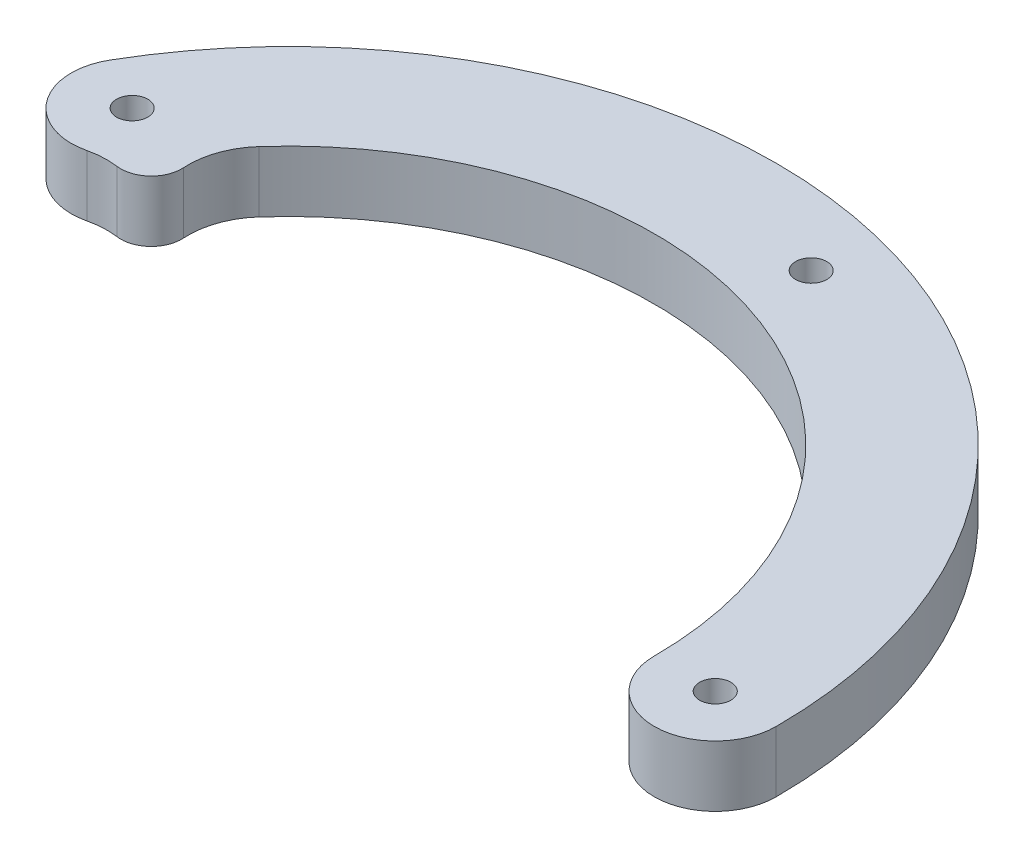
SolidWorks part; units mm, degrees
ref_plane "Front Plane" through (0, 0, 0) normal (0, 0, 1) x (1, 0, 0)
ref_plane "Top Plane" through (0, 0, 0) normal (0, 1, 0) x (1, 0, 0)
ref_plane "Right Plane" through (0, 0, 0) normal (1, 0, 0) x (0, 0, -1)
sketch "Sketch1" plane through (0, 0, 0) normal (0, 1, 0) x (1, 0, 0)
  line L3 (0, 0) -> (-30.84, 17.8055) construction
  line L4 (0, 0) -> (44.45, 0) construction
  line L5 (0, 0) -> (11.5045, 42.9354) construction
  line L6 (-35.7452, 20.6375) -> (-38.4948, 22.225) construction
  arc A0 (50.8, 0) -> (-43.9941, 25.4) centre (0, 0) ccw
  arc A1 (38.1, 0) -> (-28.4399, 25.3531) centre (0, 0) ccw
  circle A2 centre (0, 0) radius 38.1 construction
  circle A3 centre (0, 0) radius 50.8 construction
  arc A4 (-43.9941, 25.4) -> (-37.0197, 16.0487) centre (-38.4948, 22.225) ccw
  arc A5 (38.1, 0) -> (50.8, 0) centre (44.45, 0) ccw
  circle A6 centre (-38.4948, 22.225) radius 1.625
  circle A7 centre (44.45, 0) radius 1.625
  circle A8 centre (0, 0) radius 44.45 construction
  circle A9 centre (11.5045, 42.9354) radius 1.625
  arc A10 (-34.0591, 16.1913) -> (-30.4528, 19.5331) centre (-33.6217, 19.336) ccw
  arc A11 (-37.0197, 16.0487) -> (-34.0591, 16.1913) centre (-35.1613, 8.2676) cw
  arc A12 (-30.4528, 19.5331) -> (-28.4399, 25.3531) centre (-22.4683, 20.0297) cw
  dimension "D1" = 101.6
  dimension "D3" = 3.25
  dimension "D4" = 3.25
  dimension "D7" = 3.25
  dimension "D8" = 6.35
  dimension "D9" = 8
  dimension "D5" = 150
  dimension "D6" = 75
  dimension "D2" = 12.7
extrude "Boss-Extrude1" add sketch "Sketch1" along normal blind 6.35
